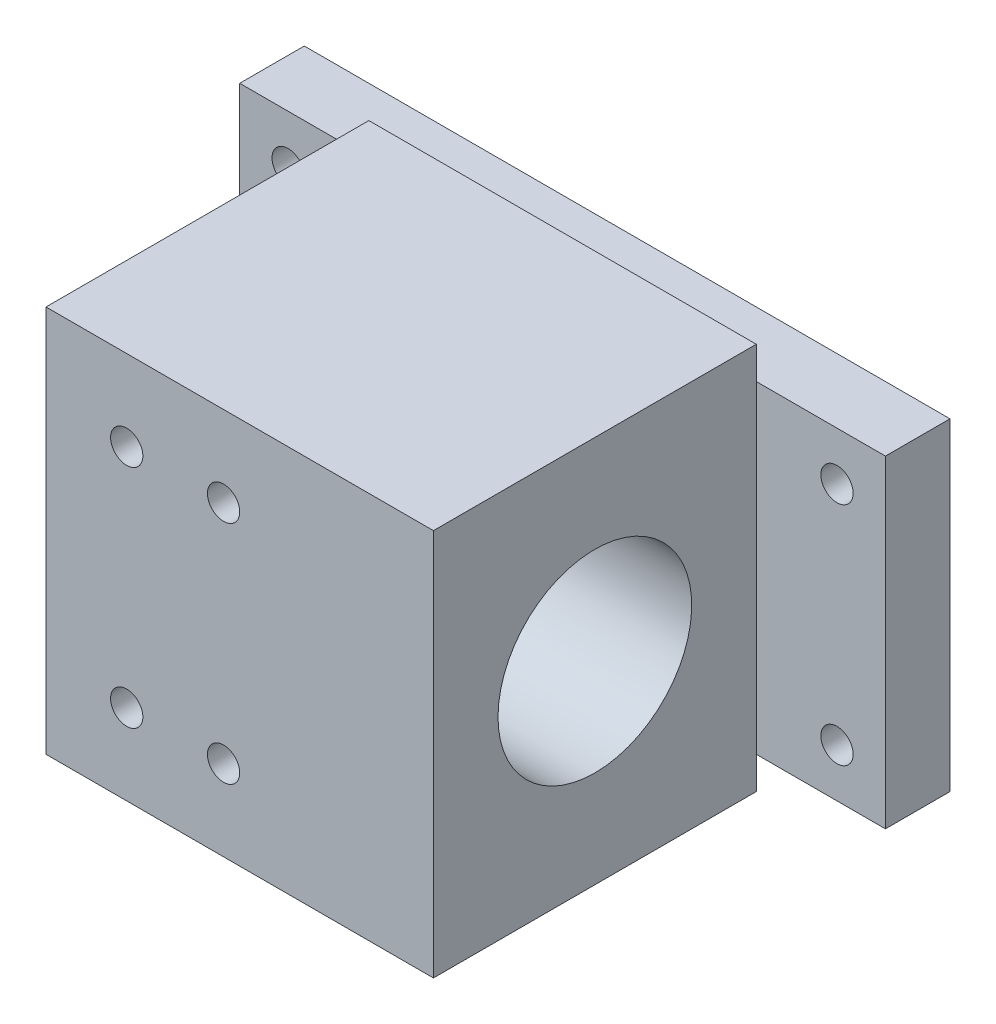
SolidWorks part; units mm, degrees
material "5052-H32"
ref_plane "Front Plane" through (0, 0, 0) normal (0, 0, 1) x (1, 0, 0)
ref_plane "Top Plane" through (0, 0, 0) normal (0, 1, 0) x (1, 0, 0)
ref_plane "Right Plane" through (0, 0, 0) normal (1, 0, 0) x (0, 0, -1)
sketch "Sketch1" plane through (0, 0, 0) normal (0, 0, 1) x (1, 0, 0)
  line L1 (-50, 25) -> (50, 25)
  line L2 (-50, 25) -> (-50, -25)
  line L3 (-50, -25) -> (50, -25)
  line L4 (50, 25) -> (50, -25)
  line L5 (-50, 25) -> (50, -25) construction
  line L6 (-50, -25) -> (50, 25) construction
  circle A0 centre (-42.5, 17.5) radius 2.5
  circle A1 centre (42.5, 17.5) radius 2.5
  circle A2 centre (42.5, -17.5) radius 2.5
  circle A3 centre (-42.5, -17.5) radius 2.5
  point P0 (0, 0)
  dimension "D3" = 5
  dimension "D4" = 5
  dimension "D5" = 5
  dimension "D6" = 5
  dimension "D1" = 100
  dimension "D2" = 50
  dimension "D7" = 35
  dimension "D8" = 35
  dimension "D9" = 85
  dimension "D10" = 85
  dimension "D11" = 7.5
  dimension "D12" = 7.5
  dimension "D13" = 7.5
  dimension "D14" = 7.5
extrude "Boss-Extrude1" add sketch "Sketch1" along normal blind 10
sketch "Sketch2" plane through (0, 0, 10) normal (0, 0, 1) x (1, 0, 0)
  line L1 (-30, 30) -> (30, 30)
  line L2 (-30, 30) -> (-30, -30)
  line L3 (-30, -30) -> (30, -30)
  line L4 (30, 30) -> (30, -30)
  line L5 (-30, 30) -> (30, -30) construction
  line L6 (-30, -30) -> (30, 30) construction
  point P0 (0, 0)
  dimension "D1" = 60
  dimension "D2" = 60
extrude "Boss-Extrude2" add sketch "Sketch2" along normal blind 50
sketch "Sketch3" plane through (-30, 0, 0) normal (-1, 0, 0) x (0, 0, 1)
  line L0 (10, 25) -> (10, -25) construction
  line L1 (60, -30) -> (10, -30) construction
  circle A0 centre (35, 0) radius 15
  dimension "D1" = 25
  dimension "D2" = 30
  dimension "D3" = 30
extrude "Cut-Extrude1" cut sketch "Sketch3" against normal blind 101
sketch "Sketch4" plane through (0, 25, 0) normal (0, 1, 0) x (1, 0, 0)
  line L0 (30, -60) -> (-30, -60) construction
  line L1 (-30, -60) -> (-30, -10) construction
  circle A0 centre (-12.5, -7.5) radius 2.5
  circle A1 centre (22.5, -7.5) radius 2.5
  circle A2 centre (22.5, -42.5) radius 2.5
  circle A4 centre (-12.5, -42.5) radius 2.5
  dimension "D1" = 35
  dimension "D5" = 5
  dimension "D2" = 35
  dimension "D3" = 17.5
  dimension "D4" = 17.5
sketch "Sketch5" plane through (0, 0, 60) normal (0, 0, 1) x (1, 0, 0)
  line L0 (30, 30) -> (-30, 30) construction
  line L2 (-30, 25) -> (-30, -25) construction
  circle A0 centre (-17.5, 17.5) radius 2.5
  circle A1 centre (-2.5, 17.5) radius 2.5
  circle A2 centre (-2.5, -17.5) radius 2.5
  circle A3 centre (-17.5, -17.5) radius 2.5
  dimension "D1" = 5
  dimension "D2" = 15
  dimension "D3" = 35
  dimension "D4" = 12.5
  dimension "D5" = 12.5
extrude "Cut-Extrude3" cut sketch "Sketch5" against normal blind 10
